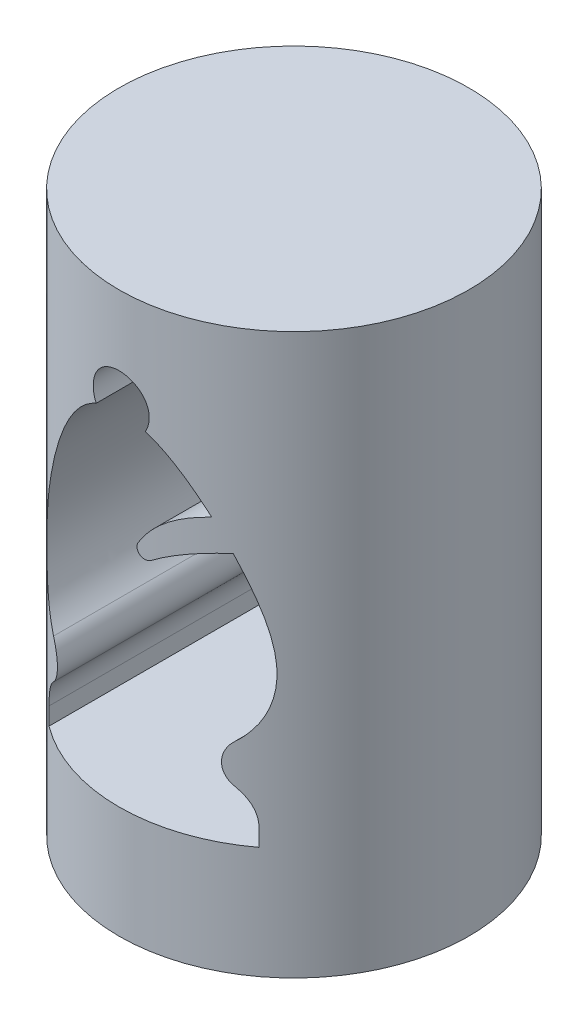
SolidWorks part; units mm, degrees
ref_plane "Front" through (0, 0, 0) normal (0, 0, 1) x (1, 0, 0)
ref_plane "Top" through (0, 0, 0) normal (0, 1, 0) x (1, 0, 0)
ref_plane "Right" through (0, 0, 0) normal (1, 0, 0) x (0, 0, -1)
sketch "Sketch2" plane through (0, 0, 0) normal (0, 1, 0) x (1, 0, 0)
  circle A0 centre (0, 0) radius 12.5
  dimension "D1" = 25
extrude "Boss-Extrude1" add sketch "Sketch2" along normal mid plane 40
sketch "Sketch3" plane through (0, 0, 0) normal (0, 0, 1) x (1, 0, 0)
  line L0 (-7.5, -12) -> (7.5, -12)
  line L1 (7.5, -12) -> (7.5, -10.75)
  line L2 (-7.5, -10.75) -> (-7.5, -12)
  line L3 (-6.5, -5.586) -> (6.5, -5.586) construction
  line L4 (-7, 4) -> (7, 4) construction
  arc A0 (7.5, -10.75) -> (6.4652, -8.3826) centre (4.2746, -10.75) ccw
  arc A4 (-6.4652, -8.3826) -> (-7.5, -10.75) centre (-4.2746, -10.75) ccw
  arc A6 (-6.5, -5.586) -> (-6.4652, -8.3826) centre (-7.7444, -7) cw
  arc A8 (6.5, -5.586) -> (6.4652, -8.3826) centre (7.7444, -7) ccw
  arc A9 (1.7547, 12.0403) -> (-1.7547, 12.0403) centre (0, 13) ccw
  arc A10 (5.4005, 8.017) -> (1.3015, 4.9775) centre (6.8739, 1.7464) ccw
  arc A11 (1.3015, 4.9775) -> (2.125, 4.2276) centre (1.7944, 4.6917) ccw
  arc A12 (2.125, 4.2276) -> (6.3991, 6.0075) centre (8.1646, -4.2534) cw
  spline S0 degree 3 poles (-6.5, -5.586) (-9.2801, -3.1393) (-7.6489, 3.3982) (-3.9563, 10.9411) (-1.7547, 12.0403) knots 0 0 0 0 0.237893 0.453263 0.453263 0.453263 0.453263
  spline S1 degree 3 poles (1.7547, 12.0403) (3.0974, 11.3969) (4.3523, 9.8783) (5.4005, 8.017) knots 0.547215 0.547215 0.547215 0.547215 0.677371 0.677371 0.677371 0.677371
  spline S2 degree 3 poles (6.3991, 6.0075) (6.6749, 5.3795) (8.4193, 0.929) (8.8666, -3.5032) (6.5, -5.586) knots 0.721905 0.721905 0.721905 0.721905 0.762107 1 1 1 1
  point P0 (0, -12)
  point P5 (0, -5.586)
  point P7 (0, 4)
  dimension "D1" = 14
  dimension "D6" = 1.25
  dimension "D7" = 5
  dimension "D9" = 4
  dimension "D2" = 15
  dimension "D4" = 13
  dimension "D5" = 12
  dimension "D8" = 16
  dimension "D10" = 13
extrude "Cut-Extrude1" cut sketch "Sketch3" against normal through all both and the other way through all
sketch "Sketch4" plane through (0, -20, 0) normal (0, -1, 0) x (-1, 0, 0)
  circle A0 centre (0, 0) radius 3
  dimension "D1" = 6
extrude "Cut-Extrude2" cut sketch "Sketch4" against normal blind 3
